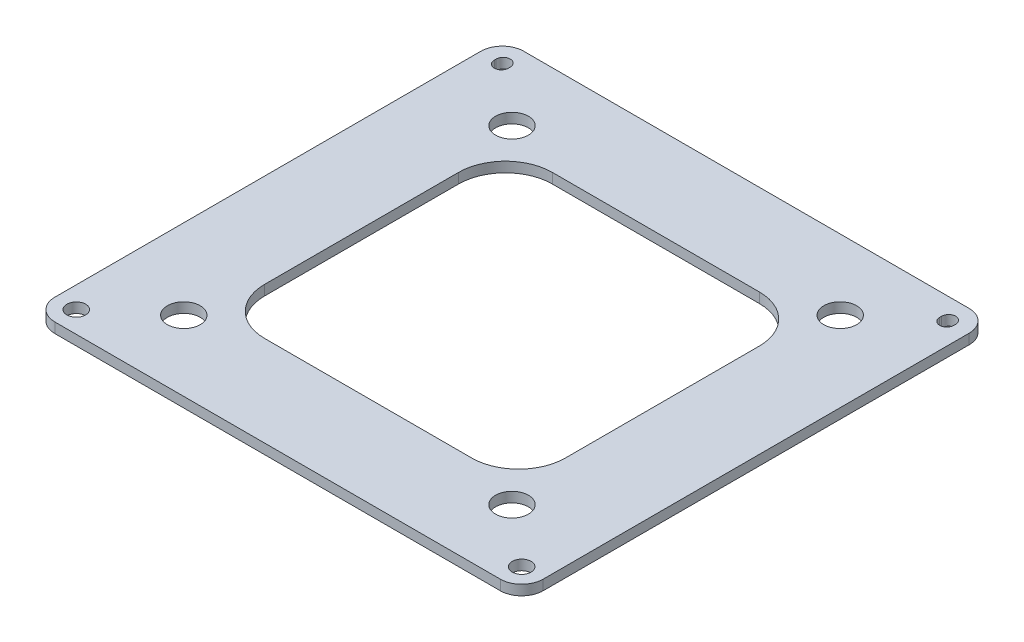
SolidWorks part; units mm, degrees
material "ABS"
ref_plane "Front Plane" through (0, 0, 0) normal (0, 0, 1) x (1, 0, 0)
ref_plane "Top Plane" through (0, 0, 0) normal (0, 1, 0) x (1, 0, 0)
ref_plane "Right Plane" through (0, 0, 0) normal (1, 0, 0) x (0, 0, -1)
sketch "Sketch2" plane through (0, 0, 0) normal (0, 1, 0) x (1, 0, 0)
  line L0 (0, 0) -> (0, 50000) construction
  line L1 (-47.5, -45.425) -> (47.5, -45.425) construction
  line L2 (-47.5, -45.425) -> (-47.5, 45.425) construction
  line L3 (-47.5, 45.425) -> (47.5, 45.425) construction
  line L4 (47.5, -45.425) -> (47.5, 45.425) construction
  line L5 (-47.5, -45.425) -> (47.5, 45.425) construction
  line L6 (-47.5, 45.425) -> (47.5, -45.425) construction
  line L7 (-49, 45.225) -> (-46, 45.225) construction
  line L8 (-49, 45.225) -> (-49, 45.625)
  line L9 (-49, 45.625) -> (-46, 45.625) construction
  line L10 (-46, 45.225) -> (-46, 45.625)
  line L11 (-49, 45.225) -> (-46, 45.625) construction
  line L12 (-49, 45.625) -> (-46, 45.225) construction
  line L13 (49, 45.625) -> (46, 45.225) construction
  line L14 (49, 45.225) -> (46, 45.625) construction
  line L15 (49, 45.625) -> (46, 45.625) construction
  line L16 (49, 45.225) -> (46, 45.225) construction
  line L17 (46, 45.225) -> (46, 45.625)
  line L18 (49, 45.225) -> (49, 45.625)
  line L19 (-52.075, 45.425) -> (-52.075, -45.425)
  line L20 (-47.5, -50) -> (47.5, -50)
  line L21 (52.075, 45.425) -> (52.075, -45.425)
  line L22 (-47.5, 50) -> (47.5, 50)
  line L24 (-22.075, -30.6738) -> (22.075, -30.6738)
  line L25 (-32.075, -20.6738) -> (-32.075, 20.6738)
  line L26 (-22.075, 30.6738) -> (22.075, 30.6738)
  line L27 (32.075, -20.6738) -> (32.075, 20.6738)
  line L28 (-32.075, -30.6738) -> (32.075, 30.6738) construction
  line L29 (-32.075, 30.6738) -> (32.075, -30.6738) construction
  line L30 (-35, -35) -> (35, -35) construction
  line L31 (-35, -35) -> (-35, 35) construction
  line L32 (-35, 35) -> (35, 35) construction
  line L33 (35, -35) -> (35, 35) construction
  line L34 (-35, -35) -> (35, 35) construction
  line L35 (-35, 35) -> (35, -35) construction
  circle A2 centre (47.5, -45.425) radius 2
  circle A3 centre (-47.5, -45.425) radius 2
  arc A4 (-46, 45.625) -> (-49, 45.625) centre (-47.5, 45.625) ccw
  arc A5 (-49, 45.225) -> (-46, 45.225) centre (-47.5, 45.225) ccw
  arc A6 (49, 45.225) -> (46, 45.225) centre (47.5, 45.225) cw
  arc A7 (46, 45.625) -> (49, 45.625) centre (47.5, 45.625) cw
  arc A8 (-52.075, -45.425) -> (-47.5, -50) centre (-47.5, -45.425) ccw
  arc A9 (-47.5, 50) -> (-52.075, 45.425) centre (-47.5, 45.425) ccw
  arc A10 (52.075, 45.425) -> (47.5, 50) centre (47.5, 45.425) ccw
  arc A11 (47.5, -50) -> (52.075, -45.425) centre (47.5, -45.425) ccw
  arc A12 (-22.075, -30.6738) -> (-32.075, -20.6738) centre (-22.075, -20.6738) cw
  arc A13 (22.075, -30.6738) -> (32.075, -20.6738) centre (22.075, -20.6738) ccw
  arc A14 (22.075, 30.6738) -> (32.075, 20.6738) centre (22.075, 20.6738) cw
  arc A15 (-32.075, 20.6738) -> (-22.075, 30.6738) centre (-22.075, 20.6738) cw
  circle A16 centre (-35, 35) radius 3.5
  circle A17 centre (35, 35) radius 3.5
  circle A18 centre (35, -35) radius 3.5
  circle A19 centre (-35, -35) radius 3.5
  point P0 (0, 0)
  point P22 (0, 0)
  point P47 (0, 0)
  dimension "D3" = 4
  dimension "D8" = 10
  dimension "D10" = 7
  dimension "D1" = 95
  dimension "D2" = 90.85
  dimension "D4" = 3
  dimension "D5" = 0.4
  dimension "D6" = 100
  dimension "D7" = 20
  dimension "D9" = 70
extrude "Boss-Extrude1" add sketch "Sketch2" along normal blind 2.15
